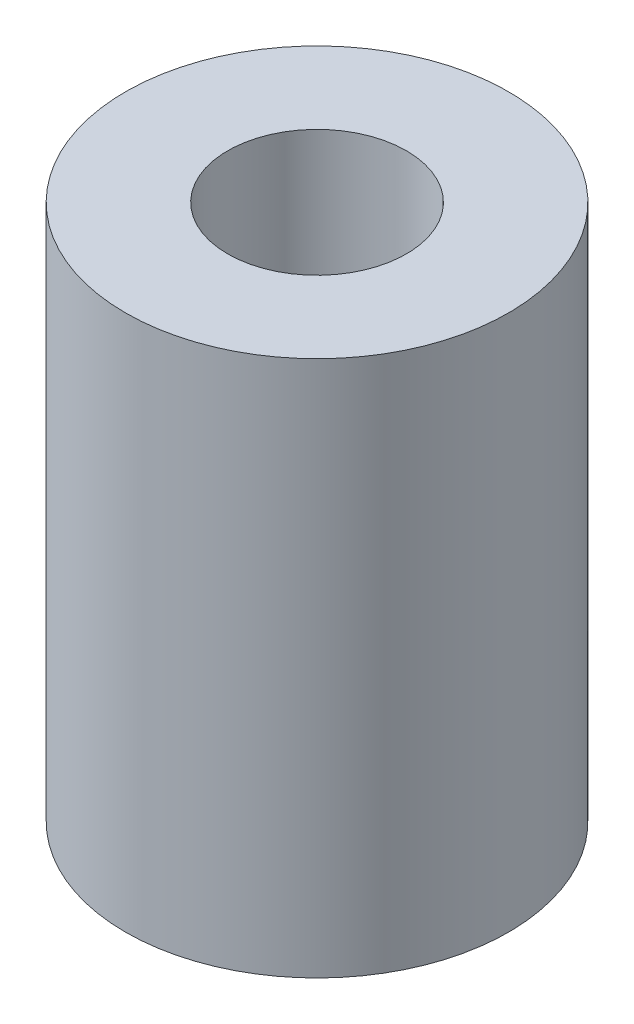
SolidWorks part; units mm, degrees
ref_plane "Front Plane" through (0, 0, 0) normal (0, 0, 1) x (1, 0, 0)
ref_plane "Top Plane" through (0, 0, 0) normal (0, 1, 0) x (1, 0, 0)
ref_plane "Right Plane" through (0, 0, 0) normal (1, 0, 0) x (0, 0, -1)
sketch "Sketch1" plane through (0, 0, 0) normal (0, 1, 0) x (1, 0, 0)
  circle A0 centre (0, 0) radius 3.75
  dimension "D1" = 7.5
extrude "Boss-Extrude1" add sketch "Sketch1" along normal blind 10.5
hole_wizard "Ø3.5 (3.5) Diameter Hole1" positions "Sketch4" profile "Sketch3" hole size "Ø3.5" standard "JIS" end condition through all
sketch "Sketch4" plane through (0, 10.5, 0) normal (0, 1, 0) x (1, 0, 0)
  point P0 (0, 0)
sketch "Sketch3" plane through (0, 10.5, 0) normal (1, 0, 0) x (0, 0, 1)
  line L0 (0, 0) -> (0, 10.5)
  line L1 (0, 10.5) -> (1.75, 10.5)
  line L2 (1.75, 10.5) -> (1.75, 0)
  line L5 (1.75, 0) -> (0, 0)
  line L11 (0, -6.35) -> (0, 107.95) construction
  dimension "Thru Hole Dia." = 3.5
  dimension "Thru Hole Depth" = 10.5
